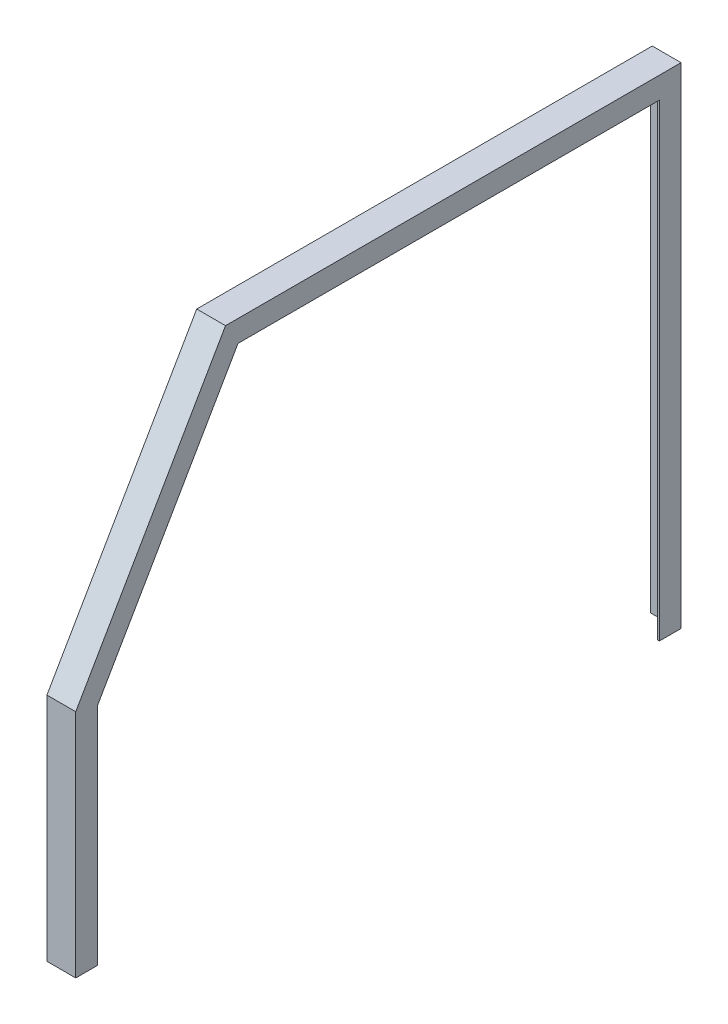
SolidWorks part; units mm, degrees
ref_plane "Front Plane" through (0, 0, 0) normal (0, 0, 1) x (1, 0, 0)
ref_plane "Top Plane" through (0, 0, 0) normal (0, 1, 0) x (1, 0, 0)
ref_plane "Right Plane" through (0, 0, 0) normal (1, 0, 0) x (0, 0, -1)
sketch "Sketch1" plane through (0, 0, 0) normal (1, 0, 0) x (0, 0, -1)
  line L0 (-495.3, 0) -> (495.3, 0) construction
  line L1 (-495.3, 0) -> (-495.3, 396.1911)
  line L2 (-495.3, 396.1911) -> (-247.4384, 825.5)
  line L3 (-247.4384, 825.5) -> (495.3, 825.5)
  line L4 (495.3, 825.5) -> (495.3, 0)
  line L5 (-495.3, 0) -> (-533.4, 0)
  line L6 (-533.4, 0) -> (-533.4, 406.4)
  line L7 (-533.4, 406.4) -> (-269.4355, 863.6)
  line L8 (-269.4355, 863.6) -> (533.4, 863.6)
  line L9 (533.4, 863.6) -> (533.4, 0)
  line L10 (533.4, 0) -> (495.3, 0)
  dimension "D1" = 38.1
  dimension "D2" = 38.1
  dimension "D3" = 38.1
  dimension "D4" = 38.1
  dimension "D5" = 1066.8
  dimension "D6" = 863.6
  dimension "D7" = 30
  dimension "D8" = 406.4
extrude "Boss-Extrude1" add sketch "Sketch1" along normal blind 3.175
sketch "Sketch2" plane through (0, 0, 0) normal (-1, 0, 0) x (0, 0, 1)
  line L1 (530.225, 0) -> (530.225, 405.5493)
  line L2 (530.225, 405.5493) -> (267.6024, 860.425)
  line L3 (267.6024, 860.425) -> (-530.225, 860.425)
  line L4 (-530.225, 860.425) -> (-530.225, 0)
  line L5 (-533.4, 0) -> (-530.225, 0)
  line L6 (530.225, 0) -> (533.4, 0)
  line L10 (495.3, 0) -> (533.4, 0)
  line L11 (533.4, 0) -> (533.4, 406.4)
  line L12 (533.4, 406.4) -> (269.4355, 863.6)
  line L13 (269.4355, 863.6) -> (-533.4, 863.6)
  line L14 (-533.4, 863.6) -> (-533.4, 0)
  line L15 (-533.4, 0) -> (-495.3, 0)
  line L16 (-495.3, 0) -> (-495.3, 825.5)
  line L17 (-495.3, 825.5) -> (247.4384, 825.5)
  line L18 (247.4384, 825.5) -> (495.3, 396.1911)
  line L19 (495.3, 396.1911) -> (495.3, 0)
  line L21 (533.4, 0) -> (533.4, 406.4)
  line L22 (533.4, 406.4) -> (269.4355, 863.6)
  line L23 (269.4355, 863.6) -> (-533.4, 863.6)
  line L24 (-533.4, 863.6) -> (-533.4, 0)
  dimension "D1" = 0
  dimension "D2" = 3.175
extrude "Boss-Extrude2" add sketch "Sketch2" along normal blind 47.625
